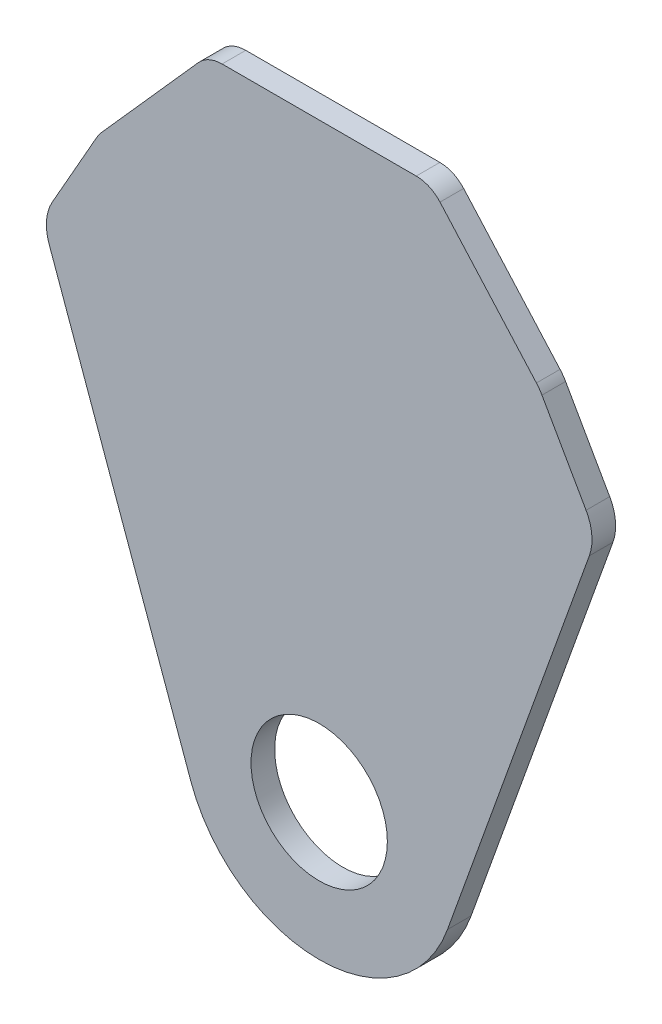
SolidWorks part; units mm, degrees
material "6061-T6 (SS)"
ref_plane "Front Plane" through (0, 0, 0) normal (0, 0, 1) x (1, 0, 0)
ref_plane "Top Plane" through (0, 0, 0) normal (0, 1, 0) x (1, 0, 0)
ref_plane "Right Plane" through (0, 0, 0) normal (1, 0, 0) x (0, 0, -1)
sketch "Sketch1" plane through (0, 0, 0) normal (0, 0, 1) x (1, 0, 0)
  line L0 (-31.115, 165.1) -> (31.115, 165.1)
  line L1 (-61.595, 130.81) -> (61.595, 130.81) construction
  line L2 (-77.47, 102.87) -> (-61.595, 130.81)
  line L3 (-77.47, 102.87) -> (77.47, 102.87) construction
  line L4 (-61.595, 130.81) -> (-31.115, 165.1)
  line L5 (31.115, 165.1) -> (61.595, 130.81)
  line L6 (-77.47, 102.87) -> (-35.8534, -12.8896)
  line L7 (77.47, 102.87) -> (61.595, 130.81)
  line L8 (77.47, 102.87) -> (35.8534, -12.8896)
  circle A0 centre (0, 0) radius 19.05
  arc A1 (-35.8534, -12.8896) -> (35.8534, -12.8896) centre (0, 0) ccw
  point P6 (0, 165.1)
  point P9 (0, 130.81)
  point P12 (0, 102.87)
  dimension "D1" = 38.1
  dimension "D2" = 76.2
  dimension "D3" = 165.1
  dimension "D4" = 62.23
  dimension "D5" = 123.19
  dimension "D6" = 154.94
  dimension "D7" = 34.29
  dimension "D8" = 27.94
extrude "Boss-Extrude1" add sketch "Sketch1" along normal blind 6.604
fillet "Fillet1" radius 12.7 4 edges at (-77.47, 102.87, 3.302) (-61.595, 130.81, 3.302) (61.595, 130.81, 3.302) (77.47, 102.87, 3.302)
fillet "Fillet2" radius 8.89 2 edges at (-31.115, 165.1, 3.302) (31.115, 165.1, 3.302)
